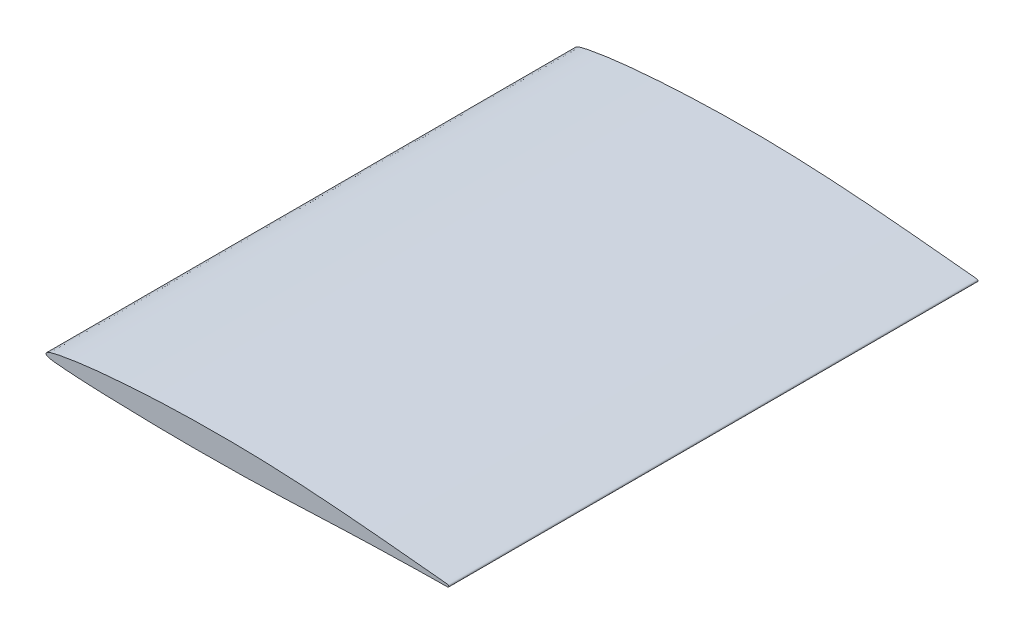
SolidWorks part; units mm, degrees
ref_plane "Ebene vorne" through (0, 0, 0) normal (0, 0, 1) x (1, 0, 0)
ref_plane "Ebene oben" through (0, 0, 0) normal (0, 1, 0) x (1, 0, 0)
ref_plane "Ebene rechts" through (0, 0, 0) normal (1, 0, 0) x (0, 0, -1)
curve "Kurve1"
  spline degree 3 poles (149.9884, -0.1466, 0) (150.0079, -0.0053, 0) (149.9795, 0.1334, 0) (149.8882, 0.2511, 0) (149.7639, 0.3542, 0) (149.6041, 0.4193, 0) (149.4286, 0.4463, 0) (149.2457, 0.4556, 0) (149.058, 0.4679, 0) (148.8662, 0.4813, 0) (148.6696, 0.5001, 0) (148.467, 0.5202, 0) (148.2576, 0.5411, 0) (148.0414, 0.5635, 0) (147.8176, 0.5851, 0) (147.586, 0.6084, 0) (147.3466, 0.6321, 0) (147.0994, 0.6576, 0) (146.8439, 0.6818, 0) (146.5801, 0.7097, 0) (146.3073, 0.7361, 0) (146.0257, 0.7644, 0) (145.7347, 0.7933, 0) (145.434, 0.8233, 0) (145.1237, 0.8543, 0) (144.8033, 0.8864, 0) (144.4727, 0.9194, 0) (144.1313, 0.953, 0) (143.7794, 0.9897, 0) (143.416, 1.0254, 0) (143.041, 1.0622, 0) (142.654, 1.1015, 0) (142.255, 1.1414, 0) (141.844, 1.1825, 0) (141.4203, 1.2243, 0) (140.9837, 1.2685, 0) (140.5334, 1.3136, 0) (140.0693, 1.3593, 0) (139.5914, 1.4076, 0) (139.0994, 1.4567, 0) (138.5929, 1.5059, 0) (138.0718, 1.5601, 0) (137.535, 1.6122, 0) (136.9826, 1.6675, 0) (136.415, 1.7247, 0) (135.831, 1.7825, 0) (135.2306, 1.8424, 0) (134.6134, 1.9047, 0) (133.9794, 1.9678, 0) (133.3279, 2.0311, 0) (132.6594, 2.0991, 0) (131.9726, 2.1654, 0) (131.268, 2.2345, 0) (130.545, 2.3058, 0) (129.8037, 2.3775, 0) (129.0437, 2.4515, 0) (128.2644, 2.5279, 0) (127.466, 2.6047, 0) (126.648, 2.6827, 0) (125.811, 2.7624, 0) (124.9541, 2.8449, 0) (124.0777, 2.9278, 0) (123.1813, 3.0115, 0) (122.2651, 3.0979, 0) (121.3287, 3.1846, 0) (120.3724, 3.2731, 0) (119.3963, 3.3604, 0) (118.4, 3.4508, 0) (117.3837, 3.5419, 0) (116.3474, 3.6326, 0) (115.2914, 3.725, 0) (114.2157, 3.8165, 0) (113.1207, 3.91, 0) (112.0063, 4.0025, 0) (110.8731, 4.0971, 0) (109.7207, 4.1897, 0) (108.5501, 4.2828, 0) (107.3614, 4.3755, 0) (106.1548, 4.4691, 0) (104.9307, 4.5603, 0) (103.6898, 4.6532, 0) (102.4324, 4.7423, 0) (101.1591, 4.8331, 0) (99.8701, 4.9205, 0) (98.5664, 5.0079, 0) (97.2484, 5.0928, 0) (95.9167, 5.1757, 0) (94.5721, 5.257, 0) (93.2154, 5.3345, 0) (91.8471, 5.4109, 0) (90.4681, 5.4837, 0) (89.0787, 5.5537, 0) (87.6808, 5.6209, 0) (86.2741, 5.6836, 0) (84.8601, 5.7439, 0) (83.4394, 5.7997, 0) (82.0131, 5.8519, 0) (80.582, 5.8993, 0) (79.1467, 5.9451, 0) (77.7087, 5.9845, 0) (76.2687, 6.021, 0) (74.8277, 6.0516, 0) (73.3867, 6.0786, 0) (71.9464, 6.1019, 0) (70.508, 6.1196, 0) (69.0724, 6.1337, 0) (67.6403, 6.1436, 0) (66.213, 6.1497, 0) (64.7913, 6.1516, 0) (63.376, 6.1498, 0) (61.968, 6.1433, 0) (60.568, 6.1352, 0) (59.1773, 6.1201, 0) (57.7963, 6.1049, 0) (56.426, 6.0849, 0) (55.067, 6.0602, 0) (53.7203, 6.0349, 0) (52.3863, 6.0049, 0) (51.066, 5.9704, 0) (49.7599, 5.9348, 0) (48.4689, 5.8958, 0) (47.1933, 5.8535, 0) (45.9333, 5.8098, 0) (44.6896, 5.7629, 0) (43.4629, 5.7125, 0) (42.2539, 5.6611, 0) (41.063, 5.6053, 0) (39.8899, 5.5503, 0) (38.7353, 5.4903, 0) (37.5995, 5.4314, 0) (36.4833, 5.3675, 0) (35.3862, 5.3041, 0) (34.3086, 5.2377, 0) (33.2506, 5.1708, 0) (32.2126, 5.1028, 0) (31.1946, 5.0339, 0) (30.1966, 4.9638, 0) (29.2189, 4.893, 0) (28.2613, 4.8206, 0) (27.3239, 4.7491, 0) (26.4062, 4.676, 0) (25.5089, 4.6018, 0) (24.6315, 4.5281, 0) (23.7743, 4.4528, 0) (22.9366, 4.3779, 0) (22.1182, 4.3031, 0) (21.3196, 4.2269, 0) (20.5403, 4.1508, 0) (19.7802, 4.0753, 0) (19.0393, 3.9975, 0) (18.3168, 3.9224, 0) (17.6129, 3.8448, 0) (16.9271, 3.7685, 0) (16.2596, 3.6896, 0) (15.6095, 3.6131, 0) (14.9769, 3.5361, 0) (14.3615, 3.4592, 0) (13.7633, 3.3816, 0) (13.1814, 3.3065, 0) (12.6159, 3.2287, 0) (12.0663, 3.1529, 0) (11.5322, 3.0783, 0) (11.0136, 3.0027, 0) (10.5098, 2.9292, 0) (10.0209, 2.8549, 0) (9.5466, 2.7819, 0) (9.0863, 2.7098, 0) (8.6396, 2.6389, 0) (8.2061, 2.5692, 0) (7.7863, 2.4986, 0) (7.3789, 2.4308, 0) (6.9838, 2.3641, 0) (6.6012, 2.297, 0) (6.2303, 2.2306, 0) (5.8711, 2.1664, 0) (5.5233, 2.1006, 0) (5.1864, 2.0371, 0) (4.8602, 1.9729, 0) (4.5444, 1.9092, 0) (4.2389, 1.8446, 0) (3.9431, 1.7822, 0) (3.6572, 1.7187, 0) (3.3803, 1.6572, 0) (3.1131, 1.594, 0) (2.8549, 1.5313, 0) (2.6061, 1.4674, 0) (2.3667, 1.401, 0) (2.1353, 1.3356, 0) (1.9133, 1.2676, 0) (1.7002, 1.1972, 0) (1.4948, 1.1267, 0) (1.2978, 1.053, 0) (1.1075, 0.9799, 0) (0.9253, 0.9023, 0) (0.7486, 0.8226, 0) (0.579, 0.7356, 0) (0.4198, 0.6389, 0) (0.2762, 0.5328, 0) (0.1568, 0.4138, 0) (0.0654, 0.2842, 0) (0.0079, 0.1451, 0) (-0.008, -0.0004, 0) (0.0249, -0.143, 0) (0.0961, -0.2758, 0) (0.2037, -0.3921, 0) (0.3394, -0.4897, 0) (0.4963, -0.5713, 0) (0.6693, -0.638, 0) (0.8498, -0.6983, 0) (1.0363, -0.7522, 0) (1.2278, -0.8023, 0) (1.426, -0.8489, 0) (1.6312, -0.8943, 0) (1.8443, -0.9362, 0) (2.0654, -0.9748, 0) (2.2947, -1.0123, 0) (2.5325, -1.0457, 0) (2.7788, -1.078, 0) (3.0336, -1.1075, 0) (3.2972, -1.1368, 0) (3.57, -1.1644, 0) (3.852, -1.1924, 0) (4.1433, -1.2206, 0) (4.444, -1.248, 0) (4.7545, -1.2781, 0) (5.0751, -1.3046, 0) (5.4059, -1.3361, 0) (5.7474, -1.364, 0) (6.0996, -1.3946, 0) (6.463, -1.4245, 0) (6.838, -1.4542, 0) (7.225, -1.4855, 0) (7.6239, -1.5168, 0) (8.035, -1.546, 0) (8.4586, -1.5777, 0) (8.8954, -1.6081, 0) (9.3456, -1.6409, 0) (9.8096, -1.6713, 0) (10.2876, -1.7026, 0) (10.7797, -1.7331, 0) (11.2863, -1.7658, 0) (11.808, -1.7964, 0) (12.345, -1.8271, 0) (12.8973, -1.8598, 0) (13.4653, -1.8903, 0) (14.0496, -1.9215, 0) (14.6503, -1.9524, 0) (15.2676, -1.9834, 0) (15.902, -2.0144, 0) (16.5536, -2.0457, 0) (17.223, -2.0753, 0) (17.91, -2.1054, 0) (18.615, -2.1354, 0) (19.3383, -2.1653, 0) (20.0803, -2.1957, 0) (20.841, -2.2243, 0) (21.6207, -2.2533, 0) (22.4193, -2.2827, 0) (23.2377, -2.3099, 0) (24.0753, -2.3396, 0) (24.9323, -2.3676, 0) (25.809, -2.3939, 0) (26.7053, -2.4226, 0) (27.6216, -2.4496, 0) (28.5577, -2.4749, 0) (29.5136, -2.5027, 0) (30.4897, -2.5281, 0) (31.4856, -2.5546, 0) (32.5017, -2.5791, 0) (33.5373, -2.6045, 0) (34.5927, -2.6281, 0) (35.6673, -2.6525, 0) (36.7613, -2.6753, 0) (37.8743, -2.6973, 0) (39.006, -2.7184, 0) (40.1563, -2.738, 0) (41.325, -2.7586, 0) (42.512, -2.7765, 0) (43.7167, -2.7922, 0) (44.9383, -2.8072, 0) (46.1767, -2.8216, 0) (47.4313, -2.8331, 0) (48.7017, -2.8445, 0) (49.9873, -2.8533, 0) (51.2873, -2.8605, 0) (52.6017, -2.865, 0) (53.9293, -2.8698, 0) (55.2697, -2.8699, 0) (56.622, -2.8704, 0) (57.9853, -2.8683, 0) (59.3597, -2.8643, 0) (60.7437, -2.8584, 0) (62.1367, -2.85, 0) (63.5373, -2.8416, 0) (64.9453, -2.8296, 0) (66.3597, -2.8139, 0) (67.7797, -2.7987, 0) (69.204, -2.7791, 0) (70.6324, -2.7586, 0) (72.0633, -2.7342, 0) (73.4964, -2.7085, 0) (74.9297, -2.6796, 0) (76.363, -2.6472, 0) (77.7954, -2.6137, 0) (79.226, -2.5763, 0) (80.654, -2.5373, 0) (82.0781, -2.4968, 0) (83.4973, -2.452, 0) (84.911, -2.4075, 0) (86.3184, -2.3604, 0) (87.7184, -2.3115, 0) (89.11, -2.2603, 0) (90.493, -2.2084, 0) (91.8664, -2.1554, 0) (93.229, -2.1015, 0) (94.58, -2.0462, 0) (95.919, -1.9913, 0) (97.2453, -1.9363, 0) (98.5587, -1.8813, 0) (99.8577, -1.8262, 0) (101.1423, -1.772, 0) (102.4117, -1.7195, 0) (103.6653, -1.6658, 0) (104.9027, -1.6153, 0) (106.1233, -1.5649, 0) (107.327, -1.5173, 0) (108.513, -1.4702, 0) (109.681, -1.424, 0) (110.831, -1.38, 0) (111.9623, -1.3382, 0) (113.075, -1.2973, 0) (114.1683, -1.2565, 0) (115.2427, -1.2206, 0) (116.2973, -1.1829, 0) (117.3326, -1.1479, 0) (118.348, -1.1153, 0) (119.3436, -1.0828, 0) (120.3193, -1.0532, 0) (121.2753, -1.0242, 0) (122.2116, -0.9958, 0) (123.128, -0.9704, 0) (124.0247, -0.9444, 0) (124.9013, -0.9176, 0) (125.7587, -0.8948, 0) (126.5963, -0.8689, 0) (127.4143, -0.8455, 0) (128.213, -0.8209, 0) (128.9927, -0.7985, 0) (129.7536, -0.7748, 0) (130.496, -0.7541, 0) (131.2197, -0.7342, 0) (131.9253, -0.7147, 0) (132.613, -0.6982, 0) (133.283, -0.6818, 0) (133.9353, -0.6679, 0) (134.5703, -0.6558, 0) (135.1887, -0.646, 0) (135.7903, -0.6371, 0) (136.3757, -0.6282, 0) (136.9447, -0.6187, 0) (137.498, -0.6115, 0) (138.0357, -0.6019, 0) (138.5583, -0.5938, 0) (139.066, -0.5875, 0) (139.5593, -0.5787, 0) (140.0383, -0.5722, 0) (140.5033, -0.5651, 0) (140.9547, -0.5581, 0) (141.3927, -0.5512, 0) (141.8177, -0.5438, 0) (142.23, -0.5382, 0) (142.63, -0.532, 0) (143.018, -0.5262, 0) (143.394, -0.5197, 0) (143.7587, -0.5155, 0) (144.112, -0.5087, 0) (144.4547, -0.5042, 0) (144.786, -0.499, 0) (145.1073, -0.4942, 0) (145.4187, -0.4887, 0) (145.7207, -0.4855, 0) (146.0127, -0.4797, 0) (146.2953, -0.4762, 0) (146.569, -0.472, 0) (146.834, -0.4681, 0) (147.0907, -0.464, 0) (147.339, -0.4602, 0) (147.5793, -0.4557, 0) (147.8117, -0.4534, 0) (148.0363, -0.4491, 0) (148.2537, -0.4447, 0) (148.4637, -0.4423, 0) (148.6673, -0.4383, 0) (148.866, -0.4385, 0) (149.0607, -0.4416, 0) (149.2513, -0.4468, 0) (149.4327, -0.4525, 0) (149.6069, -0.433, 0) (149.7649, -0.3718, 0) (149.9011, -0.2789, 0) (149.9884, -0.1466, 0) (150.0079, -0.0053, 0) (149.9795, 0.1334, 0) knots -0.001525 -0.000968 -0.000469 0 0.000414 0.000904 0.001445 0.002006 0.002592 0.003202 0.003826 0.004461 0.005113 0.005788 0.006484 0.007203 0.007948 0.008717 0.009516 0.010338 0.011187 0.012066 0.012974 0.01391 0.014878 0.01588 0.016912 0.017977 0.019079 0.020214 0.021386 0.022594 0.023842 0.02513 0.026458 0.027826 0.029234 0.030689 0.032186 0.033731 0.035322 0.036959 0.038643 0.040378 0.042165 0.044002 0.045893 0.047833 0.049834 0.051887 0.053997 0.056164 0.058391 0.060674 0.06302 0.065426 0.067891 0.07042 0.073013 0.075671 0.078389 0.081178 0.084026 0.086943 0.089924 0.092971 0.096087 0.099267 0.102513 0.105825 0.109207 0.112651 0.116162 0.119738 0.123378 0.12708 0.130849 0.134677 0.138567 0.142517 0.146523 0.150592 0.154713 0.158887 0.163117 0.167396 0.171725 0.176099 0.180519 0.184982 0.189483 0.194021 0.198598 0.203204 0.207843 0.212504 0.217195 0.221905 0.226631 0.231376 0.236131 0.240899 0.24567 0.250444 0.25522 0.25999 0.264756 0.269513 0.274255 0.278985 0.283695 0.288381 0.293048 0.297685 0.302292 0.306866 0.311407 0.315909 0.320371 0.32479 0.329167 0.333494 0.337771 0.342 0.346175 0.350298 0.354366 0.358373 0.362322 0.366212 0.370042 0.37381 0.377512 0.381151 0.384728 0.388239 0.391684 0.395064 0.398377 0.401625 0.404803 0.407919 0.410966 0.41395 0.416865 0.419714 0.422501 0.425221 0.427879 0.430472 0.433001 0.435469 0.437873 0.440219 0.442505 0.444729 0.446897 0.449009 0.451062 0.453058 0.455002 0.456891 0.45873 0.460516 0.462249 0.463936 0.465574 0.467163 0.468705 0.470204 0.471657 0.473067 0.474433 0.47576 0.477048 0.478293 0.479504 0.480674 0.48181 0.48291 0.483978 0.48501 0.486012 0.486982 0.487919 0.488831 0.489711 0.490559 0.491383 0.492179 0.492948 0.49369 0.494409 0.495105 0.49578 0.496435 0.497072 0.497706 0.498327 0.498921 0.499476 0.499995 0.500487 0.500956 0.501424 0.501919 0.502437 0.502984 0.503572 0.504189 0.504825 0.505463 0.506117 0.506791 0.507486 0.508205 0.508949 0.509717 0.510513 0.511335 0.512185 0.513061 0.51397 0.514909 0.515877 0.516878 0.517909 0.518977 0.520074 0.521211 0.522381 0.523587 0.524833 0.526119 0.527445 0.528809 0.530214 0.531665 0.533159 0.534699 0.536286 0.537919 0.539598 0.54133 0.543111 0.544942 0.546826 0.548763 0.550756 0.552803 0.554905 0.557067 0.559285 0.561562 0.563899 0.566296 0.568755 0.571278 0.573859 0.576507 0.579218 0.581995 0.584835 0.587738 0.59071 0.593745 0.596846 0.600014 0.603247 0.606547 0.609913 0.613345 0.61684 0.620402 0.624026 0.627713 0.631463 0.635272 0.639144 0.643076 0.647067 0.651115 0.655215 0.659372 0.663582 0.667838 0.672147 0.676499 0.680897 0.685338 0.689816 0.694333 0.698884 0.703471 0.708085 0.712725 0.717389 0.722075 0.726779 0.731499 0.736229 0.740972 0.745719 0.750469 0.755216 0.759964 0.764705 0.769436 0.774157 0.778859 0.783545 0.788211 0.79285 0.797464 0.802047 0.806601 0.811119 0.815597 0.820036 0.824435 0.828787 0.833096 0.837353 0.841563 0.84572 0.84982 0.853867 0.857858 0.861789 0.865661 0.869472 0.873224 0.876909 0.880535 0.884094 0.88759 0.89102 0.894387 0.897684 0.900918 0.904086 0.907187 0.910225 0.913194 0.9161 0.91894 0.921716 0.924427 0.927071 0.929655 0.932177 0.934635 0.937034 0.93937 0.941649 0.943869 0.946029 0.948132 0.950179 0.952173 0.954111 0.955996 0.957827 0.95961 0.961339 0.963021 0.964654 0.966241 0.967781 0.969275 0.970726 0.972134 0.973498 0.974823 0.976108 0.977354 0.97856 0.979732 0.980865 0.981965 0.983025 0.984058 0.985058 0.986026 0.98696 0.987867 0.988745 0.989593 0.990418 0.991213 0.991981 0.992727 0.993445 0.994141 0.994813 0.995469 0.996115 0.996748 0.997364 0.997918 0.998475 0.999032 0.999531 1 1.000414 1.000904 1.001445 periodic
sketch "Skizze1" plane through (0, 0, 0) normal (0, 0, 1) x (1, 0, 0)
  spline S0 degree 3 poles (149.9884, -0.1466) (150.0079, -0.0053) (149.9795, 0.1334) (149.8882, 0.2511) (149.7639, 0.3542) (149.6041, 0.4193) (149.4286, 0.4463) (149.2457, 0.4556) (149.058, 0.4679) (148.8662, 0.4813) (148.6696, 0.5001) (148.467, 0.5202) (148.2576, 0.5411) (148.0414, 0.5635) (147.8176, 0.5851) (147.586, 0.6084) (147.3466, 0.6321) (147.0994, 0.6576) (146.8439, 0.6818) (146.5801, 0.7097) (146.3073, 0.7361) (146.0257, 0.7644) (145.7347, 0.7933) (145.434, 0.8233) (145.1237, 0.8543) (144.8033, 0.8864) (144.4727, 0.9194) (144.1313, 0.953) (143.7794, 0.9897) (143.416, 1.0254) (143.041, 1.0622) (142.654, 1.1015) (142.255, 1.1414) (141.844, 1.1825) (141.4203, 1.2243) (140.9837, 1.2685) (140.5334, 1.3136) (140.0693, 1.3593) (139.5914, 1.4076) (139.0994, 1.4567) (138.5929, 1.5059) (138.0718, 1.5601) (137.535, 1.6122) (136.9826, 1.6675) (136.415, 1.7247) (135.831, 1.7825) (135.2306, 1.8424) (134.6134, 1.9047) (133.9794, 1.9678) (133.3279, 2.0311) (132.6594, 2.0991) (131.9726, 2.1654) (131.268, 2.2345) (130.545, 2.3058) (129.8037, 2.3775) (129.0437, 2.4515) (128.2644, 2.5279) (127.466, 2.6047) (126.648, 2.6827) (125.811, 2.7624) (124.9541, 2.8449) (124.0777, 2.9278) (123.1813, 3.0115) (122.2651, 3.0979) (121.3287, 3.1846) (120.3724, 3.2731) (119.3963, 3.3604) (118.4, 3.4508) (117.3837, 3.5419) (116.3474, 3.6326) (115.2914, 3.725) (114.2157, 3.8165) (113.1207, 3.91) (112.0063, 4.0025) (110.8731, 4.0971) (109.7207, 4.1897) (108.5501, 4.2828) (107.3614, 4.3755) (106.1548, 4.4691) (104.9307, 4.5603) (103.6898, 4.6532) (102.4324, 4.7423) (101.1591, 4.8331) (99.8701, 4.9205) (98.5664, 5.0079) (97.2484, 5.0928) (95.9167, 5.1757) (94.5721, 5.257) (93.2154, 5.3345) (91.8471, 5.4109) (90.4681, 5.4837) (89.0787, 5.5537) (87.6808, 5.6209) (86.2741, 5.6836) (84.8601, 5.7439) (83.4394, 5.7997) (82.0131, 5.8519) (80.582, 5.8993) (79.1467, 5.9451) (77.7087, 5.9845) (76.2687, 6.021) (74.8277, 6.0516) (73.3867, 6.0786) (71.9464, 6.1019) (70.508, 6.1196) (69.0724, 6.1337) (67.6403, 6.1436) (66.213, 6.1497) (64.7913, 6.1516) (63.376, 6.1498) (61.968, 6.1433) (60.568, 6.1352) (59.1773, 6.1201) (57.7963, 6.1049) (56.426, 6.0849) (55.067, 6.0602) (53.7203, 6.0349) (52.3863, 6.0049) (51.066, 5.9704) (49.7599, 5.9348) (48.4689, 5.8958) (47.1933, 5.8535) (45.9333, 5.8098) (44.6896, 5.7629) (43.4629, 5.7125) (42.2539, 5.6611) (41.063, 5.6053) (39.8899, 5.5503) (38.7353, 5.4903) (37.5995, 5.4314) (36.4833, 5.3675) (35.3862, 5.3041) (34.3086, 5.2377) (33.2506, 5.1708) (32.2126, 5.1028) (31.1946, 5.0339) (30.1966, 4.9638) (29.2189, 4.893) (28.2613, 4.8206) (27.3239, 4.7491) (26.4062, 4.676) (25.5089, 4.6018) (24.6315, 4.5281) (23.7743, 4.4528) (22.9366, 4.3779) (22.1182, 4.3031) (21.3196, 4.2269) (20.5403, 4.1508) (19.7802, 4.0753) (19.0393, 3.9975) (18.3168, 3.9224) (17.6129, 3.8448) (16.9271, 3.7685) (16.2596, 3.6896) (15.6095, 3.6131) (14.9769, 3.5361) (14.3615, 3.4592) (13.7633, 3.3816) (13.1814, 3.3065) (12.6159, 3.2287) (12.0663, 3.1529) (11.5322, 3.0783) (11.0136, 3.0027) (10.5098, 2.9292) (10.0209, 2.8549) (9.5466, 2.7819) (9.0863, 2.7098) (8.6396, 2.6389) (8.2061, 2.5692) (7.7863, 2.4986) (7.3789, 2.4308) (6.9838, 2.3641) (6.6012, 2.297) (6.2303, 2.2306) (5.8711, 2.1664) (5.5233, 2.1006) (5.1864, 2.0371) (4.8602, 1.9729) (4.5444, 1.9092) (4.2389, 1.8446) (3.9431, 1.7822) (3.6572, 1.7187) (3.3803, 1.6572) (3.1131, 1.594) (2.8549, 1.5313) (2.6061, 1.4674) (2.3667, 1.401) (2.1353, 1.3356) (1.9133, 1.2676) (1.7002, 1.1972) (1.4948, 1.1267) (1.2978, 1.053) (1.1075, 0.9799) (0.9253, 0.9023) (0.7486, 0.8226) (0.579, 0.7356) (0.4198, 0.6389) (0.2762, 0.5328) (0.1568, 0.4138) (0.0654, 0.2842) (0.0079, 0.1451) (-0.008, -0.0004) (0.0249, -0.143) (0.0961, -0.2758) (0.2037, -0.3921) (0.3394, -0.4897) (0.4963, -0.5713) (0.6693, -0.638) (0.8498, -0.6983) (1.0363, -0.7522) (1.2278, -0.8023) (1.426, -0.8489) (1.6312, -0.8943) (1.8443, -0.9362) (2.0654, -0.9748) (2.2947, -1.0123) (2.5325, -1.0457) (2.7788, -1.078) (3.0336, -1.1075) (3.2972, -1.1368) (3.57, -1.1644) (3.852, -1.1924) (4.1433, -1.2206) (4.444, -1.248) (4.7545, -1.2781) (5.0751, -1.3046) (5.4059, -1.3361) (5.7474, -1.364) (6.0996, -1.3946) (6.463, -1.4245) (6.838, -1.4542) (7.225, -1.4855) (7.6239, -1.5168) (8.035, -1.546) (8.4586, -1.5777) (8.8954, -1.6081) (9.3456, -1.6409) (9.8096, -1.6713) (10.2876, -1.7026) (10.7797, -1.7331) (11.2863, -1.7658) (11.808, -1.7964) (12.345, -1.8271) (12.8973, -1.8598) (13.4653, -1.8903) (14.0496, -1.9215) (14.6503, -1.9524) (15.2676, -1.9834) (15.902, -2.0144) (16.5536, -2.0457) (17.223, -2.0753) (17.91, -2.1054) (18.615, -2.1354) (19.3383, -2.1653) (20.0803, -2.1957) (20.841, -2.2243) (21.6207, -2.2533) (22.4193, -2.2827) (23.2377, -2.3099) (24.0753, -2.3396) (24.9323, -2.3676) (25.809, -2.3939) (26.7053, -2.4226) (27.6216, -2.4496) (28.5577, -2.4749) (29.5136, -2.5027) (30.4897, -2.5281) (31.4856, -2.5546) (32.5017, -2.5791) (33.5373, -2.6045) (34.5927, -2.6281) (35.6673, -2.6525) (36.7613, -2.6753) (37.8743, -2.6973) (39.006, -2.7184) (40.1563, -2.738) (41.325, -2.7586) (42.512, -2.7765) (43.7167, -2.7922) (44.9383, -2.8072) (46.1767, -2.8216) (47.4313, -2.8331) (48.7017, -2.8445) (49.9873, -2.8533) (51.2873, -2.8605) (52.6017, -2.865) (53.9293, -2.8698) (55.2697, -2.8699) (56.622, -2.8704) (57.9853, -2.8683) (59.3597, -2.8643) (60.7437, -2.8584) (62.1367, -2.85) (63.5373, -2.8416) (64.9453, -2.8296) (66.3597, -2.8139) (67.7797, -2.7987) (69.204, -2.7791) (70.6324, -2.7586) (72.0633, -2.7342) (73.4964, -2.7085) (74.9297, -2.6796) (76.363, -2.6472) (77.7954, -2.6137) (79.226, -2.5763) (80.654, -2.5373) (82.0781, -2.4968) (83.4973, -2.452) (84.911, -2.4075) (86.3184, -2.3604) (87.7184, -2.3115) (89.11, -2.2603) (90.493, -2.2084) (91.8664, -2.1554) (93.229, -2.1015) (94.58, -2.0462) (95.919, -1.9913) (97.2453, -1.9363) (98.5587, -1.8813) (99.8577, -1.8262) (101.1423, -1.772) (102.4117, -1.7195) (103.6653, -1.6658) (104.9027, -1.6153) (106.1233, -1.5649) (107.327, -1.5173) (108.513, -1.4702) (109.681, -1.424) (110.831, -1.38) (111.9623, -1.3382) (113.075, -1.2973) (114.1683, -1.2565) (115.2427, -1.2206) (116.2973, -1.1829) (117.3326, -1.1479) (118.348, -1.1153) (119.3436, -1.0828) (120.3193, -1.0532) (121.2753, -1.0242) (122.2116, -0.9958) (123.128, -0.9704) (124.0247, -0.9444) (124.9013, -0.9176) (125.7587, -0.8948) (126.5963, -0.8689) (127.4143, -0.8455) (128.213, -0.8209) (128.9927, -0.7985) (129.7536, -0.7748) (130.496, -0.7541) (131.2197, -0.7342) (131.9253, -0.7147) (132.613, -0.6982) (133.283, -0.6818) (133.9353, -0.6679) (134.5703, -0.6558) (135.1887, -0.646) (135.7903, -0.6371) (136.3757, -0.6282) (136.9447, -0.6187) (137.498, -0.6115) (138.0357, -0.6019) (138.5583, -0.5938) (139.066, -0.5875) (139.5593, -0.5787) (140.0383, -0.5722) (140.5033, -0.5651) (140.9547, -0.5581) (141.3927, -0.5512) (141.8177, -0.5438) (142.23, -0.5382) (142.63, -0.532) (143.018, -0.5262) (143.394, -0.5197) (143.7587, -0.5155) (144.112, -0.5087) (144.4547, -0.5042) (144.786, -0.499) (145.1073, -0.4942) (145.4187, -0.4887) (145.7207, -0.4855) (146.0127, -0.4797) (146.2953, -0.4762) (146.569, -0.472) (146.834, -0.4681) (147.0907, -0.464) (147.339, -0.4602) (147.5793, -0.4557) (147.8117, -0.4534) (148.0363, -0.4491) (148.2537, -0.4447) (148.4637, -0.4423) (148.6673, -0.4383) (148.866, -0.4385) (149.0607, -0.4416) (149.2513, -0.4468) (149.4327, -0.4525) (149.6069, -0.433) (149.7649, -0.3718) (149.9011, -0.2789) (149.9884, -0.1466) (150.0079, -0.0053) (149.9795, 0.1334) knots -0.001525 -0.000968 -0.000469 0 0.000414 0.000904 0.001445 0.002006 0.002592 0.003202 0.003826 0.004461 0.005113 0.005788 0.006484 0.007203 0.007948 0.008717 0.009516 0.010338 0.011187 0.012066 0.012974 0.01391 0.014878 0.01588 0.016912 0.017977 0.019079 0.020214 0.021386 0.022594 0.023842 0.02513 0.026458 0.027826 0.029234 0.030689 0.032186 0.033731 0.035322 0.036959 0.038643 0.040378 0.042165 0.044002 0.045893 0.047833 0.049834 0.051887 0.053997 0.056164 0.058391 0.060674 0.06302 0.065426 0.067891 0.07042 0.073013 0.075671 0.078389 0.081178 0.084026 0.086943 0.089924 0.092971 0.096087 0.099267 0.102513 0.105825 0.109207 0.112651 0.116162 0.119738 0.123378 0.12708 0.130849 0.134677 0.138567 0.142517 0.146523 0.150592 0.154713 0.158887 0.163117 0.167396 0.171725 0.176099 0.180519 0.184982 0.189483 0.194021 0.198598 0.203204 0.207843 0.212504 0.217195 0.221905 0.226631 0.231376 0.236131 0.240899 0.24567 0.250444 0.25522 0.25999 0.264756 0.269513 0.274255 0.278985 0.283695 0.288381 0.293048 0.297685 0.302292 0.306866 0.311407 0.315909 0.320371 0.32479 0.329167 0.333494 0.337771 0.342 0.346175 0.350298 0.354366 0.358373 0.362322 0.366212 0.370042 0.37381 0.377512 0.381151 0.384728 0.388239 0.391684 0.395064 0.398377 0.401625 0.404803 0.407919 0.410966 0.41395 0.416865 0.419714 0.422501 0.425221 0.427879 0.430472 0.433001 0.435469 0.437873 0.440219 0.442505 0.444729 0.446897 0.449009 0.451062 0.453058 0.455002 0.456891 0.45873 0.460516 0.462249 0.463936 0.465574 0.467163 0.468705 0.470204 0.471657 0.473067 0.474433 0.47576 0.477048 0.478293 0.479504 0.480674 0.48181 0.48291 0.483978 0.48501 0.486012 0.486982 0.487919 0.488831 0.489711 0.490559 0.491383 0.492179 0.492948 0.49369 0.494409 0.495105 0.49578 0.496435 0.497072 0.497706 0.498327 0.498921 0.499476 0.499995 0.500487 0.500956 0.501424 0.501919 0.502437 0.502984 0.503572 0.504189 0.504825 0.505463 0.506117 0.506791 0.507486 0.508205 0.508949 0.509717 0.510513 0.511335 0.512185 0.513061 0.51397 0.514909 0.515877 0.516878 0.517909 0.518977 0.520074 0.521211 0.522381 0.523587 0.524833 0.526119 0.527445 0.528809 0.530214 0.531665 0.533159 0.534699 0.536286 0.537919 0.539598 0.54133 0.543111 0.544942 0.546826 0.548763 0.550756 0.552803 0.554905 0.557067 0.559285 0.561562 0.563899 0.566296 0.568755 0.571278 0.573859 0.576507 0.579218 0.581995 0.584835 0.587738 0.59071 0.593745 0.596846 0.600014 0.603247 0.606547 0.609913 0.613345 0.61684 0.620402 0.624026 0.627713 0.631463 0.635272 0.639144 0.643076 0.647067 0.651115 0.655215 0.659372 0.663582 0.667838 0.672147 0.676499 0.680897 0.685338 0.689816 0.694333 0.698884 0.703471 0.708085 0.712725 0.717389 0.722075 0.726779 0.731499 0.736229 0.740972 0.745719 0.750469 0.755216 0.759964 0.764705 0.769436 0.774157 0.778859 0.783545 0.788211 0.79285 0.797464 0.802047 0.806601 0.811119 0.815597 0.820036 0.824435 0.828787 0.833096 0.837353 0.841563 0.84572 0.84982 0.853867 0.857858 0.861789 0.865661 0.869472 0.873224 0.876909 0.880535 0.884094 0.88759 0.89102 0.894387 0.897684 0.900918 0.904086 0.907187 0.910225 0.913194 0.9161 0.91894 0.921716 0.924427 0.927071 0.929655 0.932177 0.934635 0.937034 0.93937 0.941649 0.943869 0.946029 0.948132 0.950179 0.952173 0.954111 0.955996 0.957827 0.95961 0.961339 0.963021 0.964654 0.966241 0.967781 0.969275 0.970726 0.972134 0.973498 0.974823 0.976108 0.977354 0.97856 0.979732 0.980865 0.981965 0.983025 0.984058 0.985058 0.986026 0.98696 0.987867 0.988745 0.989593 0.990418 0.991213 0.991981 0.992727 0.993445 0.994141 0.994813 0.995469 0.996115 0.996748 0.997364 0.997918 0.998475 0.999032 0.999531 1 1.000414 1.000904 1.001445 only from (150, 0) to (150, 0) construction
  spline S1 degree 3 poles (149.9884, -0.1466) (150.0079, -0.0053) (149.9795, 0.1334) (149.8882, 0.2511) (149.7639, 0.3542) (149.6041, 0.4193) (149.4286, 0.4463) (149.2457, 0.4556) (149.058, 0.4679) (148.8662, 0.4813) (148.6696, 0.5001) (148.467, 0.5202) (148.2576, 0.5411) (148.0414, 0.5635) (147.8176, 0.5851) (147.586, 0.6084) (147.3466, 0.6321) (147.0994, 0.6576) (146.8439, 0.6818) (146.5801, 0.7097) (146.3073, 0.7361) (146.0257, 0.7644) (145.7347, 0.7933) (145.434, 0.8233) (145.1237, 0.8543) (144.8033, 0.8864) (144.4727, 0.9194) (144.1313, 0.953) (143.7794, 0.9897) (143.416, 1.0254) (143.041, 1.0622) (142.654, 1.1015) (142.255, 1.1414) (141.844, 1.1825) (141.4203, 1.2243) (140.9837, 1.2685) (140.5334, 1.3136) (140.0693, 1.3593) (139.5914, 1.4076) (139.0994, 1.4567) (138.5929, 1.5059) (138.0718, 1.5601) (137.535, 1.6122) (136.9826, 1.6675) (136.415, 1.7247) (135.831, 1.7825) (135.2306, 1.8424) (134.6134, 1.9047) (133.9794, 1.9678) (133.3279, 2.0311) (132.6594, 2.0991) (131.9726, 2.1654) (131.268, 2.2345) (130.545, 2.3058) (129.8037, 2.3775) (129.0437, 2.4515) (128.2644, 2.5279) (127.466, 2.6047) (126.648, 2.6827) (125.811, 2.7624) (124.9541, 2.8449) (124.0777, 2.9278) (123.1813, 3.0115) (122.2651, 3.0979) (121.3287, 3.1846) (120.3724, 3.2731) (119.3963, 3.3604) (118.4, 3.4508) (117.3837, 3.5419) (116.3474, 3.6326) (115.2914, 3.725) (114.2157, 3.8165) (113.1207, 3.91) (112.0063, 4.0025) (110.8731, 4.0971) (109.7207, 4.1897) (108.5501, 4.2828) (107.3614, 4.3755) (106.1548, 4.4691) (104.9307, 4.5603) (103.6898, 4.6532) (102.4324, 4.7423) (101.1591, 4.8331) (99.8701, 4.9205) (98.5664, 5.0079) (97.2484, 5.0928) (95.9167, 5.1757) (94.5721, 5.257) (93.2154, 5.3345) (91.8471, 5.4109) (90.4681, 5.4837) (89.0787, 5.5537) (87.6808, 5.6209) (86.2741, 5.6836) (84.8601, 5.7439) (83.4394, 5.7997) (82.0131, 5.8519) (80.582, 5.8993) (79.1467, 5.9451) (77.7087, 5.9845) (76.2687, 6.021) (74.8277, 6.0516) (73.3867, 6.0786) (71.9464, 6.1019) (70.508, 6.1196) (69.0724, 6.1337) (67.6403, 6.1436) (66.213, 6.1497) (64.7913, 6.1516) (63.376, 6.1498) (61.968, 6.1433) (60.568, 6.1352) (59.1773, 6.1201) (57.7963, 6.1049) (56.426, 6.0849) (55.067, 6.0602) (53.7203, 6.0349) (52.3863, 6.0049) (51.066, 5.9704) (49.7599, 5.9348) (48.4689, 5.8958) (47.1933, 5.8535) (45.9333, 5.8098) (44.6896, 5.7629) (43.4629, 5.7125) (42.2539, 5.6611) (41.063, 5.6053) (39.8899, 5.5503) (38.7353, 5.4903) (37.5995, 5.4314) (36.4833, 5.3675) (35.3862, 5.3041) (34.3086, 5.2377) (33.2506, 5.1708) (32.2126, 5.1028) (31.1946, 5.0339) (30.1966, 4.9638) (29.2189, 4.893) (28.2613, 4.8206) (27.3239, 4.7491) (26.4062, 4.676) (25.5089, 4.6018) (24.6315, 4.5281) (23.7743, 4.4528) (22.9366, 4.3779) (22.1182, 4.3031) (21.3196, 4.2269) (20.5403, 4.1508) (19.7802, 4.0753) (19.0393, 3.9975) (18.3168, 3.9224) (17.6129, 3.8448) (16.9271, 3.7685) (16.2596, 3.6896) (15.6095, 3.6131) (14.9769, 3.5361) (14.3615, 3.4592) (13.7633, 3.3816) (13.1814, 3.3065) (12.6159, 3.2287) (12.0663, 3.1529) (11.5322, 3.0783) (11.0136, 3.0027) (10.5098, 2.9292) (10.0209, 2.8549) (9.5466, 2.7819) (9.0863, 2.7098) (8.6396, 2.6389) (8.2061, 2.5692) (7.7863, 2.4986) (7.3789, 2.4308) (6.9838, 2.3641) (6.6012, 2.297) (6.2303, 2.2306) (5.8711, 2.1664) (5.5233, 2.1006) (5.1864, 2.0371) (4.8602, 1.9729) (4.5444, 1.9092) (4.2389, 1.8446) (3.9431, 1.7822) (3.6572, 1.7187) (3.3803, 1.6572) (3.1131, 1.594) (2.8549, 1.5313) (2.6061, 1.4674) (2.3667, 1.401) (2.1353, 1.3356) (1.9133, 1.2676) (1.7002, 1.1972) (1.4948, 1.1267) (1.2978, 1.053) (1.1075, 0.9799) (0.9253, 0.9023) (0.7486, 0.8226) (0.579, 0.7356) (0.4198, 0.6389) (0.2762, 0.5328) (0.1568, 0.4138) (0.0654, 0.2842) (0.0079, 0.1451) (-0.008, -0.0004) (0.0249, -0.143) (0.0961, -0.2758) (0.2037, -0.3921) (0.3394, -0.4897) (0.4963, -0.5713) (0.6693, -0.638) (0.8498, -0.6983) (1.0363, -0.7522) (1.2278, -0.8023) (1.426, -0.8489) (1.6312, -0.8943) (1.8443, -0.9362) (2.0654, -0.9748) (2.2947, -1.0123) (2.5325, -1.0457) (2.7788, -1.078) (3.0336, -1.1075) (3.2972, -1.1368) (3.57, -1.1644) (3.852, -1.1924) (4.1433, -1.2206) (4.444, -1.248) (4.7545, -1.2781) (5.0751, -1.3046) (5.4059, -1.3361) (5.7474, -1.364) (6.0996, -1.3946) (6.463, -1.4245) (6.838, -1.4542) (7.225, -1.4855) (7.6239, -1.5168) (8.035, -1.546) (8.4586, -1.5777) (8.8954, -1.6081) (9.3456, -1.6409) (9.8096, -1.6713) (10.2876, -1.7026) (10.7797, -1.7331) (11.2863, -1.7658) (11.808, -1.7964) (12.345, -1.8271) (12.8973, -1.8598) (13.4653, -1.8903) (14.0496, -1.9215) (14.6503, -1.9524) (15.2676, -1.9834) (15.902, -2.0144) (16.5536, -2.0457) (17.223, -2.0753) (17.91, -2.1054) (18.615, -2.1354) (19.3383, -2.1653) (20.0803, -2.1957) (20.841, -2.2243) (21.6207, -2.2533) (22.4193, -2.2827) (23.2377, -2.3099) (24.0753, -2.3396) (24.9323, -2.3676) (25.809, -2.3939) (26.7053, -2.4226) (27.6216, -2.4496) (28.5577, -2.4749) (29.5136, -2.5027) (30.4897, -2.5281) (31.4856, -2.5546) (32.5017, -2.5791) (33.5373, -2.6045) (34.5927, -2.6281) (35.6673, -2.6525) (36.7613, -2.6753) (37.8743, -2.6973) (39.006, -2.7184) (40.1563, -2.738) (41.325, -2.7586) (42.512, -2.7765) (43.7167, -2.7922) (44.9383, -2.8072) (46.1767, -2.8216) (47.4313, -2.8331) (48.7017, -2.8445) (49.9873, -2.8533) (51.2873, -2.8605) (52.6017, -2.865) (53.9293, -2.8698) (55.2697, -2.8699) (56.622, -2.8704) (57.9853, -2.8683) (59.3597, -2.8643) (60.7437, -2.8584) (62.1367, -2.85) (63.5373, -2.8416) (64.9453, -2.8296) (66.3597, -2.8139) (67.7797, -2.7987) (69.204, -2.7791) (70.6324, -2.7586) (72.0633, -2.7342) (73.4964, -2.7085) (74.9297, -2.6796) (76.363, -2.6472) (77.7954, -2.6137) (79.226, -2.5763) (80.654, -2.5373) (82.0781, -2.4968) (83.4973, -2.452) (84.911, -2.4075) (86.3184, -2.3604) (87.7184, -2.3115) (89.11, -2.2603) (90.493, -2.2084) (91.8664, -2.1554) (93.229, -2.1015) (94.58, -2.0462) (95.919, -1.9913) (97.2453, -1.9363) (98.5587, -1.8813) (99.8577, -1.8262) (101.1423, -1.772) (102.4117, -1.7195) (103.6653, -1.6658) (104.9027, -1.6153) (106.1233, -1.5649) (107.327, -1.5173) (108.513, -1.4702) (109.681, -1.424) (110.831, -1.38) (111.9623, -1.3382) (113.075, -1.2973) (114.1683, -1.2565) (115.2427, -1.2206) (116.2973, -1.1829) (117.3326, -1.1479) (118.348, -1.1153) (119.3436, -1.0828) (120.3193, -1.0532) (121.2753, -1.0242) (122.2116, -0.9958) (123.128, -0.9704) (124.0247, -0.9444) (124.9013, -0.9176) (125.7587, -0.8948) (126.5963, -0.8689) (127.4143, -0.8455) (128.213, -0.8209) (128.9927, -0.7985) (129.7536, -0.7748) (130.496, -0.7541) (131.2197, -0.7342) (131.9253, -0.7147) (132.613, -0.6982) (133.283, -0.6818) (133.9353, -0.6679) (134.5703, -0.6558) (135.1887, -0.646) (135.7903, -0.6371) (136.3757, -0.6282) (136.9447, -0.6187) (137.498, -0.6115) (138.0357, -0.6019) (138.5583, -0.5938) (139.066, -0.5875) (139.5593, -0.5787) (140.0383, -0.5722) (140.5033, -0.5651) (140.9547, -0.5581) (141.3927, -0.5512) (141.8177, -0.5438) (142.23, -0.5382) (142.63, -0.532) (143.018, -0.5262) (143.394, -0.5197) (143.7587, -0.5155) (144.112, -0.5087) (144.4547, -0.5042) (144.786, -0.499) (145.1073, -0.4942) (145.4187, -0.4887) (145.7207, -0.4855) (146.0127, -0.4797) (146.2953, -0.4762) (146.569, -0.472) (146.834, -0.4681) (147.0907, -0.464) (147.339, -0.4602) (147.5793, -0.4557) (147.8117, -0.4534) (148.0363, -0.4491) (148.2537, -0.4447) (148.4637, -0.4423) (148.6673, -0.4383) (148.866, -0.4385) (149.0607, -0.4416) (149.2513, -0.4468) (149.4327, -0.4525) (149.6069, -0.433) (149.7649, -0.3718) (149.9011, -0.2789) (149.9884, -0.1466) (150.0079, -0.0053) (149.9795, 0.1334) knots -0.001525 -0.000968 -0.000469 0 0.000414 0.000904 0.001445 0.002006 0.002592 0.003202 0.003826 0.004461 0.005113 0.005788 0.006484 0.007203 0.007948 0.008717 0.009516 0.010338 0.011187 0.012066 0.012974 0.01391 0.014878 0.01588 0.016912 0.017977 0.019079 0.020214 0.021386 0.022594 0.023842 0.02513 0.026458 0.027826 0.029234 0.030689 0.032186 0.033731 0.035322 0.036959 0.038643 0.040378 0.042165 0.044002 0.045893 0.047833 0.049834 0.051887 0.053997 0.056164 0.058391 0.060674 0.06302 0.065426 0.067891 0.07042 0.073013 0.075671 0.078389 0.081178 0.084026 0.086943 0.089924 0.092971 0.096087 0.099267 0.102513 0.105825 0.109207 0.112651 0.116162 0.119738 0.123378 0.12708 0.130849 0.134677 0.138567 0.142517 0.146523 0.150592 0.154713 0.158887 0.163117 0.167396 0.171725 0.176099 0.180519 0.184982 0.189483 0.194021 0.198598 0.203204 0.207843 0.212504 0.217195 0.221905 0.226631 0.231376 0.236131 0.240899 0.24567 0.250444 0.25522 0.25999 0.264756 0.269513 0.274255 0.278985 0.283695 0.288381 0.293048 0.297685 0.302292 0.306866 0.311407 0.315909 0.320371 0.32479 0.329167 0.333494 0.337771 0.342 0.346175 0.350298 0.354366 0.358373 0.362322 0.366212 0.370042 0.37381 0.377512 0.381151 0.384728 0.388239 0.391684 0.395064 0.398377 0.401625 0.404803 0.407919 0.410966 0.41395 0.416865 0.419714 0.422501 0.425221 0.427879 0.430472 0.433001 0.435469 0.437873 0.440219 0.442505 0.444729 0.446897 0.449009 0.451062 0.453058 0.455002 0.456891 0.45873 0.460516 0.462249 0.463936 0.465574 0.467163 0.468705 0.470204 0.471657 0.473067 0.474433 0.47576 0.477048 0.478293 0.479504 0.480674 0.48181 0.48291 0.483978 0.48501 0.486012 0.486982 0.487919 0.488831 0.489711 0.490559 0.491383 0.492179 0.492948 0.49369 0.494409 0.495105 0.49578 0.496435 0.497072 0.497706 0.498327 0.498921 0.499476 0.499995 0.500487 0.500956 0.501424 0.501919 0.502437 0.502984 0.503572 0.504189 0.504825 0.505463 0.506117 0.506791 0.507486 0.508205 0.508949 0.509717 0.510513 0.511335 0.512185 0.513061 0.51397 0.514909 0.515877 0.516878 0.517909 0.518977 0.520074 0.521211 0.522381 0.523587 0.524833 0.526119 0.527445 0.528809 0.530214 0.531665 0.533159 0.534699 0.536286 0.537919 0.539598 0.54133 0.543111 0.544942 0.546826 0.548763 0.550756 0.552803 0.554905 0.557067 0.559285 0.561562 0.563899 0.566296 0.568755 0.571278 0.573859 0.576507 0.579218 0.581995 0.584835 0.587738 0.59071 0.593745 0.596846 0.600014 0.603247 0.606547 0.609913 0.613345 0.61684 0.620402 0.624026 0.627713 0.631463 0.635272 0.639144 0.643076 0.647067 0.651115 0.655215 0.659372 0.663582 0.667838 0.672147 0.676499 0.680897 0.685338 0.689816 0.694333 0.698884 0.703471 0.708085 0.712725 0.717389 0.722075 0.726779 0.731499 0.736229 0.740972 0.745719 0.750469 0.755216 0.759964 0.764705 0.769436 0.774157 0.778859 0.783545 0.788211 0.79285 0.797464 0.802047 0.806601 0.811119 0.815597 0.820036 0.824435 0.828787 0.833096 0.837353 0.841563 0.84572 0.84982 0.853867 0.857858 0.861789 0.865661 0.869472 0.873224 0.876909 0.880535 0.884094 0.88759 0.89102 0.894387 0.897684 0.900918 0.904086 0.907187 0.910225 0.913194 0.9161 0.91894 0.921716 0.924427 0.927071 0.929655 0.932177 0.934635 0.937034 0.93937 0.941649 0.943869 0.946029 0.948132 0.950179 0.952173 0.954111 0.955996 0.957827 0.95961 0.961339 0.963021 0.964654 0.966241 0.967781 0.969275 0.970726 0.972134 0.973498 0.974823 0.976108 0.977354 0.97856 0.979732 0.980865 0.981965 0.983025 0.984058 0.985058 0.986026 0.98696 0.987867 0.988745 0.989593 0.990418 0.991213 0.991981 0.992727 0.993445 0.994141 0.994813 0.995469 0.996115 0.996748 0.997364 0.997918 0.998475 0.999032 0.999531 1 1.000414 1.000904 1.001445 only from (150, 0) to (150, 0)
extrude "Aufsatz-Linear austragen1" add sketch "Skizze1" along normal blind 197
